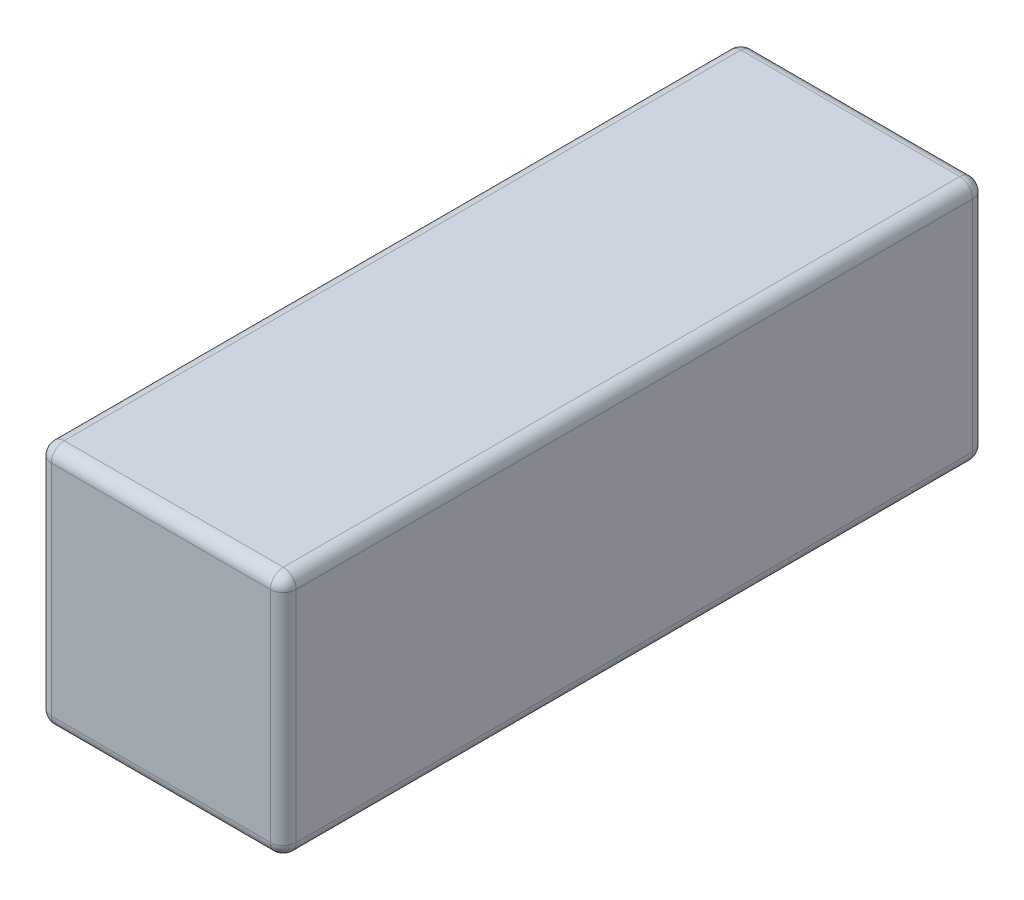
SolidWorks part; units mm, degrees
ref_plane "Front Plane" through (0, 0, 0) normal (0, 0, 1) x (1, 0, 0)
ref_plane "Top Plane" through (0, 0, 0) normal (0, 1, 0) x (1, 0, 0)
ref_plane "Right Plane" through (0, 0, 0) normal (1, 0, 0) x (0, 0, -1)
sketch "Sketch1" plane through (0, 0, 0) normal (0, 0, 1) x (1, 0, 0)
  line L1 (24.13, -24.13) -> (-24.13, -24.13)
  line L2 (24.13, -24.13) -> (24.13, 24.13)
  line L3 (24.13, 24.13) -> (-24.13, 24.13)
  line L4 (-24.13, -24.13) -> (-24.13, 24.13)
  line L5 (24.13, -24.13) -> (-24.13, 24.13) construction
  line L6 (24.13, 24.13) -> (-24.13, -24.13) construction
  point P0 (0, 0)
  dimension "D1" = 48.26
extrude "Boss-Extrude1" add sketch "Sketch1" along normal blind 138.43
fillet "Fillet1" radius 2.54 4 edges at (-24.13, -24.13, 69.215) (24.13, -24.13, 69.215) (24.13, 24.13, 69.215) (-24.13, 24.13, 69.215)
fillet "Fillet2" radius 2.54 16 edges at (23.3861, 23.3861, 0) (24.13, 0, 0) (23.3861, -23.3861, 0) (0, -24.13, 0) (-23.3861, -23.3861, 0) (-24.13, 0, 0) (-23.3861, 23.3861, 0) (-23.3861, 23.3861, 138.43) (0, 24.13, 138.43) (23.3861, 23.3861, 138.43) (24.13, 0, 138.43) (23.3861, -23.3861, 138.43) (0, -24.13, 138.43) (-23.3861, -23.3861, 138.43) (-24.13, 0, 138.43) (0, 24.13, 0)
scale "Scale1" scale about centroid uniform scaling yes scale factor 0.06
